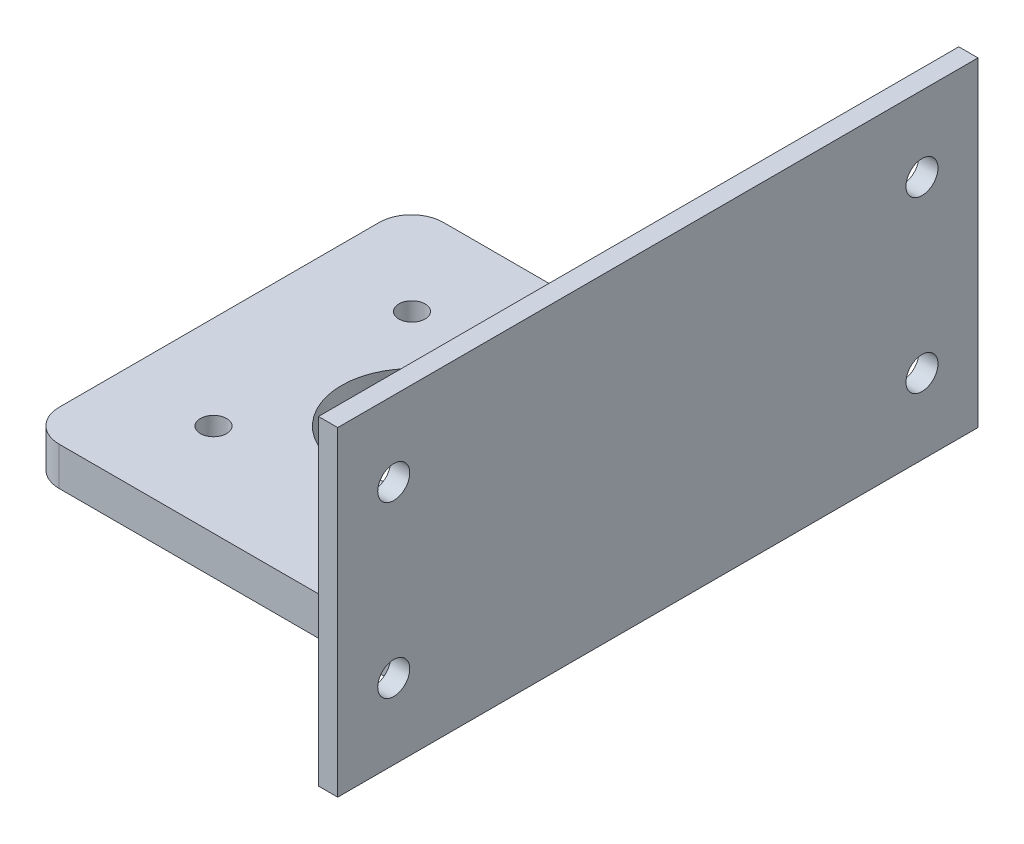
SolidWorks part; units mm, degrees
ref_plane "前视基准面" through (0, 0, 0) normal (0, 0, 1) x (1, 0, 0)
ref_plane "上视基准面" through (0, 0, 0) normal (0, 1, 0) x (1, 0, 0)
ref_plane "右视基准面" through (0, 0, 0) normal (1, 0, 0) x (0, 0, -1)
sketch "草图1" plane through (0, 0, 0) normal (0, 0, 1) x (1, 0, 0)
  line L0 (0, 0) -> (68.5, 0)
  line L1 (68.5, 0) -> (68.5, 50)
  line L2 (68.5, 50) -> (65.5, 50)
  line L3 (65.5, 50) -> (65.5, 7)
  line L4 (65.5, 7) -> (64.5, 6)
  line L5 (64.5, 6) -> (0, 6)
  line L6 (0, 6) -> (0, 0)
  dimension "D1" = 68.5
  dimension "D2" = 50
  dimension "D3" = 45
  dimension "D4" = 6
  dimension "D5" = 3
  dimension "D6" = 1
extrude "凸台-拉伸1" add sketch "草图1" along normal blind 60
sketch "草图4" plane through (0, 6, 0) normal (0, 1, 0) x (1, 0, 0)
  line L0 (0, -30) -> (68.5, -30) construction
  line L1 (0, -60) -> (0, 0) construction
  line L2 (68.5, -60) -> (68.5, 0) construction
  line L3 (30.1, 0) -> (30.1, -60) construction
  line L4 (64.5, 0) -> (0, 0) construction
  line L5 (64.5, -60) -> (0, -60) construction
  line L7 (14.6, -14.5) -> (45.6, -14.5) construction
  line L8 (14.6, -14.5) -> (14.6, -45.5) construction
  line L9 (14.6, -45.5) -> (45.6, -45.5) construction
  line L10 (45.6, -14.5) -> (45.6, -45.5) construction
  line L11 (14.6, -14.5) -> (45.6, -45.5) construction
  line L12 (14.6, -45.5) -> (45.6, -14.5) construction
  circle A0 centre (30.1, -30) radius 11
  circle A1 centre (14.6, -14.5) radius 2.05
  circle A2 centre (45.6, -14.5) radius 2.05
  circle A3 centre (45.6, -45.5) radius 2.05
  circle A4 centre (14.6, -45.5) radius 2.05
  point P27 (30.1, -30)
  dimension "D2" = 4.1
  dimension "D4" = 22
  dimension "D1" = 38.4
  dimension "D3" = 31
  dimension "D5" = 4
extrude "切除-拉伸3" cut sketch "草图4" against normal through all
fillet "圆角2" radius 5 2 edges at (0, 3, 60) (0, 3, 0)
sketch "草图5" plane through (65.5, 0, 0) normal (-1, 0, 0) x (0, 0, 1)
  line L0 (30, 50) -> (30, 0) construction
  line L1 (60, 50) -> (0, 50) construction
  line L2 (55, 0) -> (5, 0) construction
  line L3 (80, 25) -> (-20, 25) construction
  line L4 (80, 0) -> (-20, 0)
  line L5 (80, 0) -> (80, 50)
  line L6 (80, 50) -> (-20, 50)
  line L7 (-20, 0) -> (-20, 50)
  line L8 (80, 0) -> (-20, 50) construction
  line L9 (80, 50) -> (-20, 0) construction
  circle A0 centre (71.25, 11.75) radius 2.5
  circle A1 centre (-11.25, 11.75) radius 2.5
  circle A2 centre (-11.25, 38.25) radius 2.5
  circle A3 centre (71.25, 38.25) radius 2.5
  point P6 (30, 25)
  dimension "D3" = 26.5
  dimension "D4" = 82.5
  dimension "D5" = 5
  dimension "D1" = 100
  dimension "D2" = 50
extrude "凸台-拉伸2" add sketch "草图5" against normal up to surface (3 mm away) up to face at (68.5, 25, 30)
